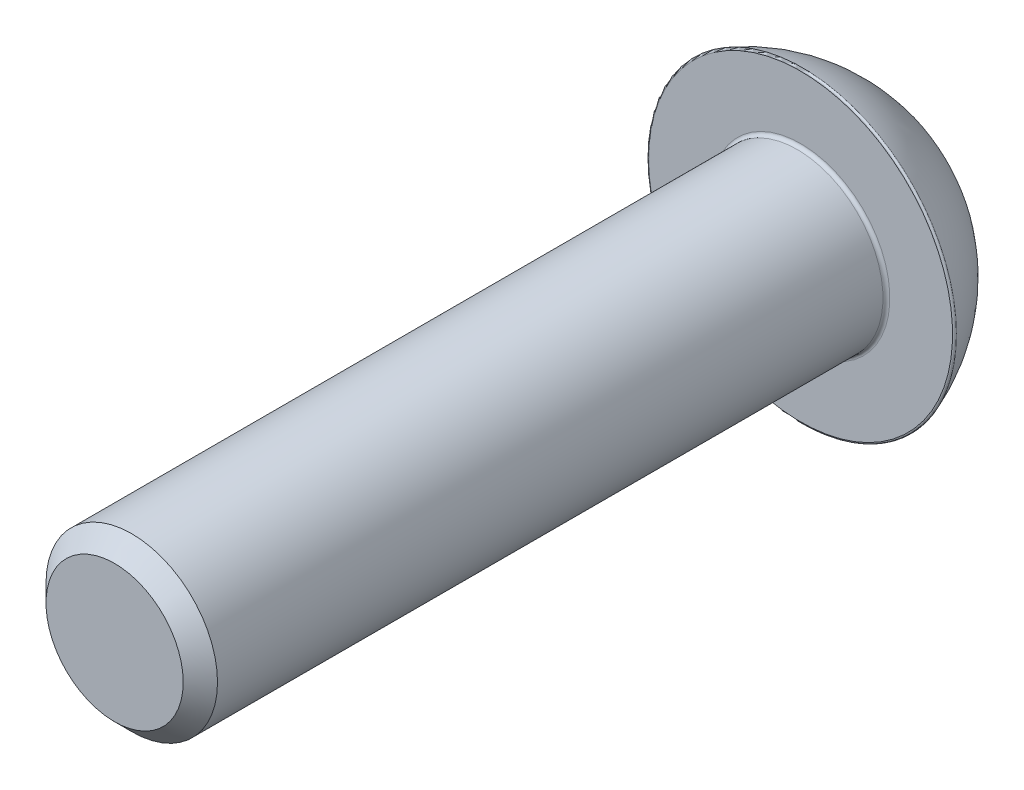
SolidWorks part; units mm, degrees
ref_plane "Piano frontale" through (0, 0, 0) normal (0, 0, 1) x (1, 0, 0)
ref_plane "Piano superiore" through (0, 0, 0) normal (0, 1, 0) x (1, 0, 0)
ref_plane "Piano destro" through (0, 0, 0) normal (1, 0, 0) x (0, 0, -1)
sketch "Schizzo1" plane through (0, 0, 0) normal (0, 0, 1) x (1, 0, 0)
  circle A0 centre (0, 0) radius 2.5
extrude "Estrusione-Estrusione1" add sketch "Schizzo1" along normal blind 20
sketch "Schizzo3" plane through (0, 0, 0) normal (1, 0, 0) x (0, 0, -1)
  line L0 (0, 0) -> (0, 4.5)
  line L1 (0, 0) -> (2.5, 0)
  line L2 (2.5, 0) -> (2.5, 2.5)
  arc A0 (0, 4.5) -> (2.5, 2.5) centre (-1.6084, -0.0731) cw
revolve "Rivoluzione1" add sketch "Schizzo3" angle 360 about L1
sketch "Schizzo4" plane through (0, 0, -2.5) normal (0, 0, -1) x (-1, 0, 0)
  line L0 (0, 2) -> (-1.7321, 1)
  line L1 (-1.7321, 1) -> (-1.7321, -1)
  line L2 (-1.7321, -1) -> (0, -2)
  line L3 (0, -2) -> (1.7321, -1)
  line L4 (1.7321, -1) -> (1.7321, 1)
  line L5 (1.7321, 1) -> (0, 2)
extrude "Taglio-Estrusione1" cut sketch "Schizzo4" against normal blind 2
sketch "Schizzo5" plane through (0, 0, 0) normal (0, 1, 0) x (1, 0, 0)
  line L0 (0, 0) -> (0, 4.4627) construction
  line L1 (-2, 2.5) -> (-2, 2.9303)
  line L2 (-2, 2.9303) -> (-1.036, 2.9303)
  line L4 (-2, 2.5) -> (-1.75, 2.25)
  line L6 (-1.036, 2.9303) -> (-1.036, 2.25)
  line L7 (-1.036, 2.25) -> (-1.75, 2.25)
revolve "Taglia-Rivoluzione2" cut sketch "Schizzo5" angle 360 about L0
fillet "Raccordo1" radius 0.1 1 edges at (2.5, 0, 0)
chamfer "Smusso1" distance 0.5 angle 45 1 edges at (2.5, 0, 20)
fillet "Raccordo2" radius 0.2 1 edges at (2.5, 0, -2.5)
fillet "Raccordo3" radius 0.05 1 edges at (4.5, 0, 0)
